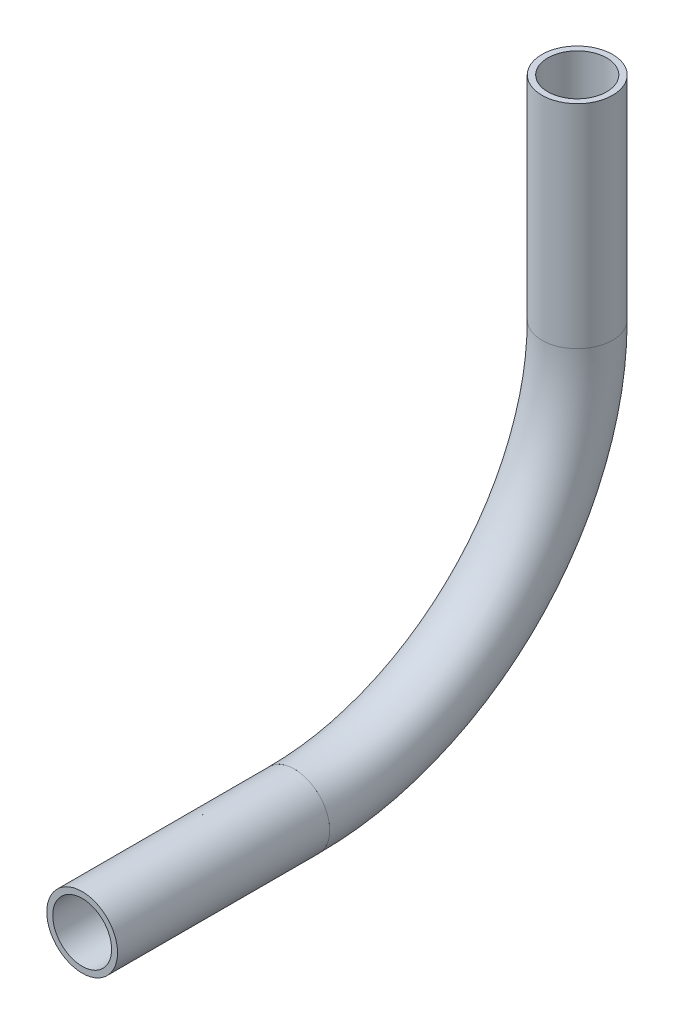
SolidWorks part; units mm, degrees
ref_plane "Front Plane" through (0, 0, 0) normal (0, 0, 1) x (1, 0, 0)
ref_plane "Top Plane" through (0, 0, 0) normal (0, 1, 0) x (1, 0, 0)
ref_plane "Right Plane" through (0, 0, 0) normal (1, 0, 0) x (0, 0, -1)
sketch "Sketch1" plane through (0, 0, 0) normal (1, 0, 0) x (0, 0, -1)
  line L0 (-192.4291, -127.0739) -> (-192.4291, -165.1739)
  line L1 (-243.2291, -215.9739) -> (-281.3291, -215.9739)
  arc A0 (-192.4291, -165.1739) -> (-243.2291, -215.9739) centre (-243.2291, -165.1739) cw
  dimension "D1" = 50.8
  dimension "D2" = 38.1
  dimension "D3" = 38.1
other "Pipe 0.5 SCH 40(1)"
ref_plane "Plane1" through (0, -127.0739, 192.4291) normal (0, -1, 0) x (0, 0, -1)
sketch "Sketch11" plane through (0, -127.0739, 192.4291) normal (0, -1, 0) x (0, 0, -1)
  circle A0 centre (0, 0) radius 5.2832
  circle A1 centre (0, 0) radius 6.35
  point P5 (0, 0)
  dimension "In_dia" = 10.5664
  dimension "Out_dia" = 12.7
